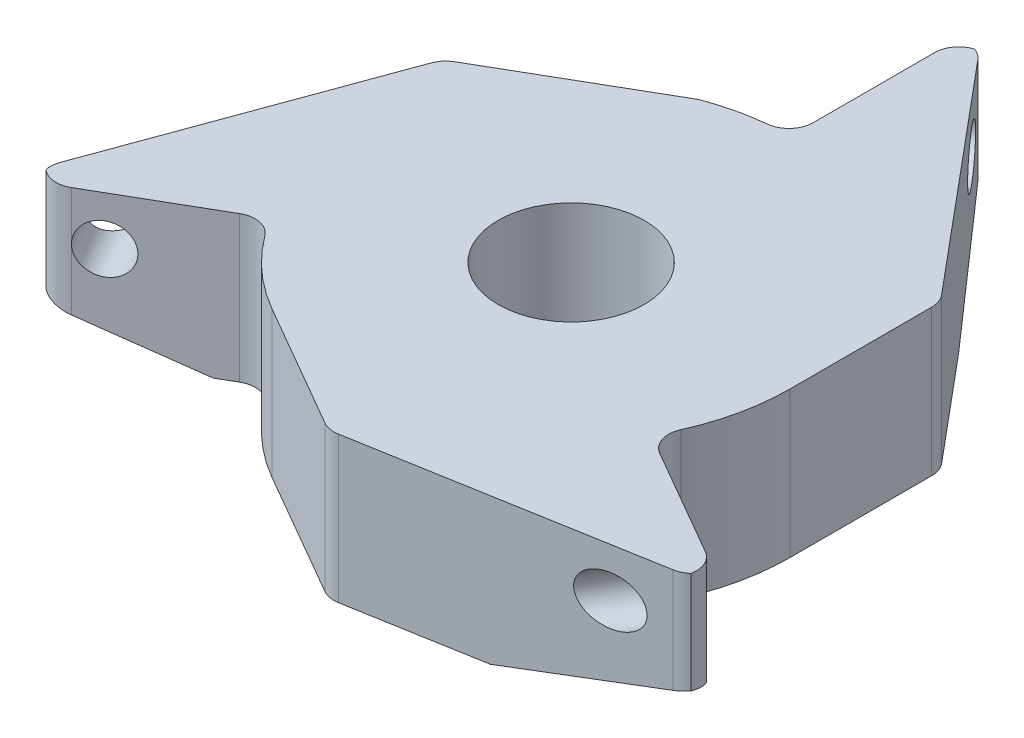
SolidWorks part; units mm, degrees
material "6061 Alloy"
ref_plane "Front Plane" through (0, 0, 0) normal (0, 0, 1) x (1, 0, 0)
ref_plane "Top Plane" through (0, 0, 0) normal (0, 1, 0) x (1, 0, 0)
ref_plane "Right Plane" through (0, 0, 0) normal (1, 0, 0) x (0, 0, -1)
sketch "Sketch1" plane through (0, 0, 0) normal (0, 1, 0) x (1, 0, 0)
  line L0 (0, 9.9499) -> (0, 14.9315)
  line L2 (1.141, 15.5732) -> (8.767, 6.4581)
  line L3 (9, 5.8165) -> (9, 0)
  line L4 (8.6168, -4.9749) -> (13.0497, -7.5342)
  line L6 (13.0349, -8.8432) -> (1.3281, -10.89)
  line L7 (0.6559, -10.771) -> (-4.5, -7.7942)
  line L8 (-8.5466, -5.0714) -> (-12.9311, -7.6027)
  line L10 (-14.0573, -6.9354) -> (-9.9764, 4.2264)
  line L11 (-9.5372, 4.749) -> (-3.1793, 8.4198)
  circle A0 centre (0, 0) radius 3
  arc A1 (-7.2419, -5.3437) -> (-4.5, -7.7942) centre (0, 0) ccw
  arc A2 (-0.9, 8.9549) -> (-3.1793, 8.4198) centre (0, 0) ccw
  arc A3 (8.2052, -3.698) -> (9, 0) centre (0, 0) ccw
  arc A4 (1.3281, -10.89) -> (0.6559, -10.771) centre (1.1559, -9.9049) cw
  arc A5 (13.5287, -8.6041) -> (13.0349, -8.8432) centre (12.8627, -7.8582) cw
  arc A6 (13.0497, -7.5342) -> (13.5287, -8.6041) centre (12.5497, -8.4003) cw
  arc A7 (8.2052, -3.698) -> (8.6168, -4.9749) centre (9.1168, -4.1089) ccw
  arc A8 (8.767, 6.4581) -> (9, 5.8165) centre (8, 5.8165) cw
  arc A9 (0.687, 15.8813) -> (1.141, 15.5732) centre (0.374, 14.9315) cw
  arc A10 (0, 14.9315) -> (0.687, 15.8813) centre (1, 14.9315) cw
  arc A11 (-7.2419, -5.3437) -> (-8.5466, -5.0714) centre (-8.0466, -5.9374) ccw
  arc A12 (-12.9311, -7.6027) -> (-14.0971, -7.4827) centre (-13.4311, -6.7367) cw
  arc A13 (-14.0573, -6.9354) -> (-14.0971, -7.4827) centre (-13.1181, -7.2788) ccw
  arc A14 (-9.5372, 4.749) -> (-9.9764, 4.2264) centre (-9.0372, 3.883) ccw
  arc A15 (0, 9.9499) -> (-0.9, 8.9549) centre (-1, 9.9499) cw
  point P22 (0.0395, -0.0685)
  point P43 (0, 9)
  dimension "D1" = 3
  dimension "D2" = 1
  dimension "D4" = 9
extrude "Boss-Extrude1" add sketch "Sketch1" along normal blind 6
sketch "Sketch2" plane through (0.0593, 0, 0.1027) normal (0.5, 0, 0.866) x (0.866, 0, -0.5)
  line L0 (-15, 6) -> (-9.9372, 6) construction
  line L2 (-16.3337, 1.9231) -> (-10.0569, -0.2316)
  line L3 (-10.0569, -0.2316) -> (-16.3337, -0.2316)
  line L4 (-16.3337, -0.2316) -> (-16.3337, 1.9231)
  circle A0 centre (-14, 4) radius 1
  dimension "D1" = 2
  dimension "D2" = 2
  dimension "D3" = 14
extrude "Cut-Extrude1" cut sketch "Sketch2" against normal through all
pattern_circular "CirPattern1" count 3 over 360 about axis through (0, 0, 0) along (0, 1, 0) of "Cut-Extrude1"
